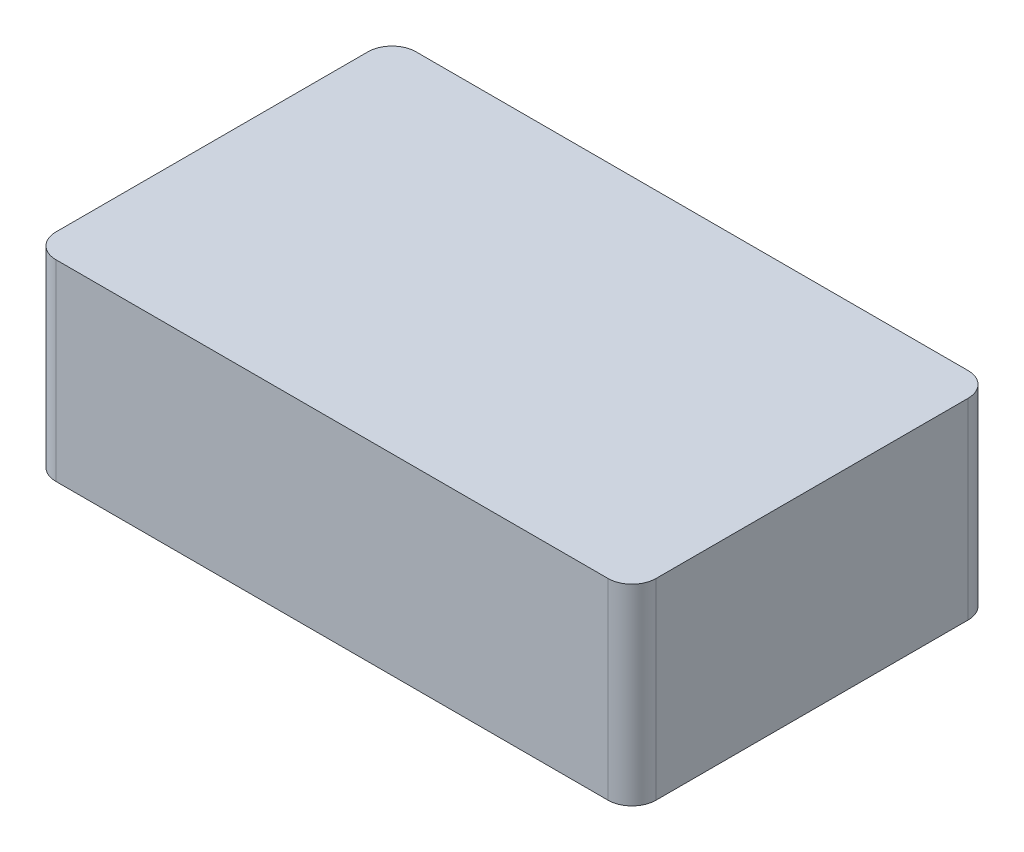
SolidWorks part; units mm, degrees
material "ABS PC"
ref_plane "Front Plane" through (0, 0, 0) normal (0, 0, 1) x (1, 0, 0)
ref_plane "Top Plane" through (0, 0, 0) normal (0, 1, 0) x (1, 0, 0)
ref_plane "Right Plane" through (0, 0, 0) normal (1, 0, 0) x (0, 0, -1)
sketch "Sketch1" plane through (0, 0, 0) normal (0, 1, 0) x (1, 0, 0)
  line L1 (100, 90.4023) -> (-130, 90.4023)
  line L2 (110, 80.4023) -> (110, -49.5977)
  line L3 (100, -59.5977) -> (-130, -59.5977)
  line L4 (-140, 80.4023) -> (-140, -49.5977)
  line L5 (110, 90.4023) -> (-140, -59.5977) construction
  line L6 (110, -59.5977) -> (-140, 90.4023) construction
  arc A0 (100, 90.4023) -> (110, 80.4023) centre (100, 80.4023) cw
  arc A1 (110, -49.5977) -> (100, -59.5977) centre (100, -49.5977) cw
  arc A2 (-130, -59.5977) -> (-140, -49.5977) centre (-130, -49.5977) cw
  arc A3 (-130, 90.4023) -> (-140, 80.4023) centre (-130, 80.4023) ccw
  point P1 (-15, 15.4023)
  dimension "D1" = 10
extrude "Boss-Extrude1" add sketch "Sketch1" along normal blind 80
